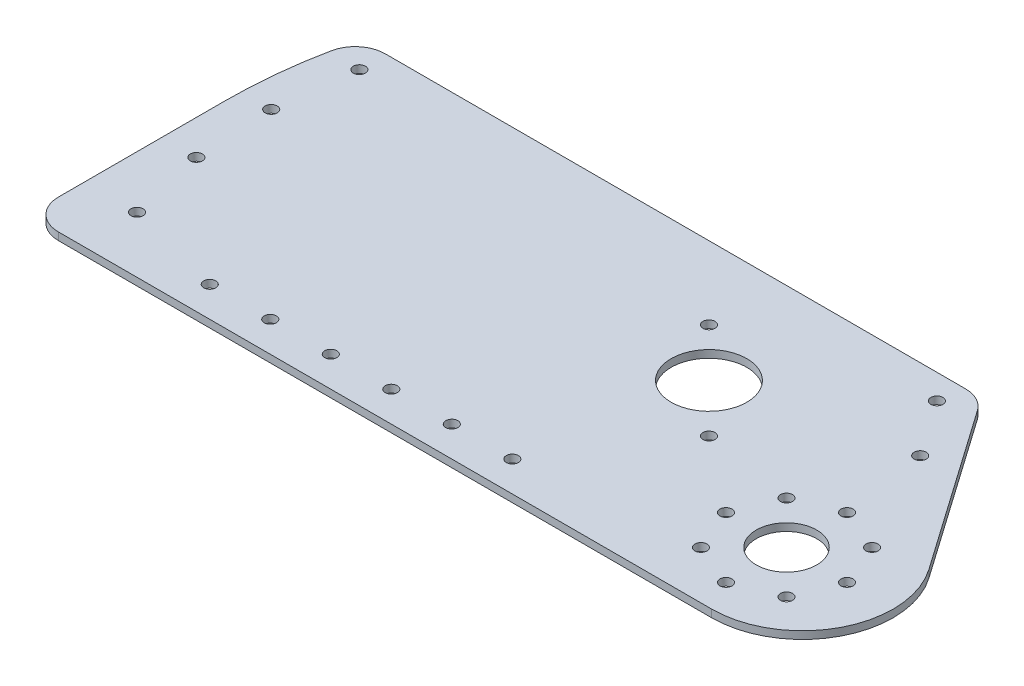
SolidWorks part; units mm, degrees
material "6061 Alloy"
ref_plane "Front Plane" through (0, 0, 0) normal (0, 0, 1) x (1, 0, 0)
ref_plane "Top Plane" through (0, 0, 0) normal (0, 1, 0) x (1, 0, 0)
ref_plane "Right Plane" through (0, 0, 0) normal (1, 0, 0) x (0, 0, -1)
sketch "Sketch1" plane through (0, 0, 0) normal (0, 1, 0) x (1, 0, 0)
  line L0 (0, 0) -> (76.9897, -44.45) construction
  line L1 (0, 0) -> (0, 50.8) construction
  line L2 (-186.6511, 50.8) -> (56.8888, 50.8)
  line L3 (67.292, 45.3844) -> (114.8929, -22.5967)
  line L4 (83.6833, -82.55) -> (-190.5, -82.55)
  line L5 (-203.2, 0) -> (-203.2, -69.85)
  circle A0 centre (0, 0) radius 15.875
  circle A1 centre (76.9897, -44.45) radius 12.7
  arc A3 (67.292, 45.3844) -> (56.8888, 50.8) centre (56.8888, 38.1) ccw
  arc A4 (-199.0945, 40.64) -> (-203.2, 0) centre (0, 0) ccw
  arc A5 (-186.6511, 50.8) -> (-199.0945, 40.64) centre (-186.6511, 38.1) ccw
  circle A6 centre (0, 0) radius 50.8 construction
  arc A7 (-190.5, -82.55) -> (-203.2, -69.85) centre (-190.5, -69.85) cw
  arc A9 (83.6833, -82.55) -> (114.8929, -22.5967) centre (83.6833, -44.45) ccw
  point P9 (97.2008, -16.2467)
  point P14 (63.5, 50.8)
  point P21 (97.2008, -16.2467)
  point P22 (97.2008, -16.2467)
  point P23 (100.6837, -22.3507)
  point P24 (121.1013, -6.8013)
  point P25 (179.646, -65.346)
  point P26 (76.9897, -82.55)
  point P27 (0, 0)
  point P28 (76.9897, -82.55)
  point P29 (152.7563, -82.55)
  point P30 (197.1461, -82.55)
  point P31 (194.4461, -80.1461)
  point P32 (203.3465, -82.55)
  point P33 (196.7823, -82.55)
  point P34 (197.9022, -82.55)
  dimension "D1" = 31.75
  dimension "D3" = 25.4
  dimension "D9" = 125
  dimension "D10" = 12.7
  dimension "D11" = 12.7
  dimension "D12" = 12.7
  dimension "FlyWheel Diameter" = 101.6
  dimension "D7" = 38.1
  dimension "D2" = 88.9
  dimension "D4" = 30
  dimension "D5" = 50.8
  dimension "D6" = 63.5
  dimension "D8" = 38.1
  dimension "BallGapAndBack" = 152.4
extrude "Initial Plate" add sketch "Sketch1" along normal blind 3.175
sketch "Sketch2" plane through (0, 3.175, 0) normal (0, 1, 0) x (1, 0, 0)
  line L0 (47.9962, 50.8) -> (104.4897, -29.8812) construction
  line L1 (114.8929, -22.5967) -> (67.292, 45.3844) construction
  line L2 (56.8888, 50.8) -> (-186.6511, 50.8) construction
  line L3 (104.4897, -29.8812) -> (114.8929, -22.5967) construction
  circle A0 centre (55.2806, 40.3968) radius 2.54
  point P6 (97.4464, -21.9982)
  point P8 (99.69, -20.682)
  point P9 (0, 0)
  point P14 (0, 0)
  point P16 (0, 0)
  dimension "ShooterFrontSupportBoltHole" = 5.08
  dimension "D1" = 12.7
  dimension "D2" = 12.7
extrude "Initial Hole Front" cut sketch "Sketch2" against normal through all
pattern_linear "Front Support Mounts" count 2 spacing 28.575 along (0.5736, 0, 0.8192) of "Initial Hole Front"
sketch "Sketch3" plane through (0, 3.175, 0) normal (0, 1, 0) x (1, 0, 0)
  line L0 (59.0291, -26.4895) -> (94.9502, -62.4105) construction
  line L1 (51.5897, -44.45) -> (102.3897, -44.45) construction
  circle A0 centre (76.9897, -44.45) radius 25.4 construction
  circle A1 centre (59.0291, -26.4895) radius 2.54
  circle A2 centre (102.3897, -44.45) radius 2.54
  circle A3 centre (94.9502, -62.4105) radius 2.54
  circle A4 centre (51.5897, -44.45) radius 2.54
  dimension "D1" = 50.8
  dimension "D2" = 45
  dimension "D3" = 5.08
extrude "Max Planetary Holes" cut sketch "Sketch3" against normal through all
pattern_circular "Max Planetary Pattern" count 3 every 90 about axis through (76.9897, 0, 44.45) along (0, 1, 0) of "Max Planetary Holes"
sketch "Sketch4" plane through (0, 3.175, 0) normal (0, 1, 0) x (1, 0, 0)
  line L0 (-202.171, 20.4234) -> (-176.8996, 17.8705) construction
  line L1 (-50.8, 0) -> (-177.8, 0) construction
  line L2 (-194.6833, 47.9374) -> (-186.3399, 39.594) construction
  line L3 (-203.2, 0) -> (-203.2, -69.85) construction
  line L4 (-203.2, 0) -> (-203.2, -69.85) construction
  circle A0 centre (0, 0) radius 177.8 construction
  arc A1 (-199.0945, 40.64) -> (-203.2, 0) centre (0, 0) ccw construction
  circle A2 centre (0, 0) radius 190.5 construction
  circle A3 centre (-186.3399, 39.594) radius 2.54
  arc A4 (-186.6511, 50.8) -> (-199.0945, 40.64) centre (-186.6511, 38.1) ccw construction
  circle A5 centre (0, 0) radius 50.8 construction
  point P9 (-189.5353, 19.147)
  point P21 (-114.3, 0)
  dimension "D1" = 25.4
  dimension "D2" = 5.08
  dimension "D4" = 101.6
  dimension "D3" = 45
  dimension "Ball Center Dist" = 88.9
extrude "Initial Static Hood Mount" cut sketch "Sketch4" against normal through all
pattern_circular "Hood Mounting Pattern" count 4 every 10 about axis through (0, 0, 0) along (0, 1, 0) of "Initial Static Hood Mount"
sketch "Sketch5" plane through (0, 3.175, 0) normal (0, 1, 0) x (1, 0, 0)
  line L0 (-190.5, -69.85) -> (83.6833, -69.85) construction
  line L1 (-190.5, -82.55) -> (83.6833, -82.55) construction
  line L2 (-190.5, -69.85) -> (-190.5, -82.55) construction
  line L3 (83.6833, -82.55) -> (83.6833, -69.85) construction
  line L4 (-203.2, 0) -> (-203.2, -69.85) construction
  circle A0 centre (-139.7, -69.85) radius 2.54
  point P7 (62.9161, -76.2)
  point P8 (0, 0)
  dimension "D2" = 5.08
  dimension "D1" = 12.7
  dimension "D3" = 63.5
extrude "Initial Mounting Hole" cut sketch "Sketch5" against normal through all
pattern_linear "Mounting Pattern" count 6 spacing 25.4 along (1, 0, 0) of "Initial Mounting Hole"
sketch "Sketch6" plane through (0, 3.175, 0) normal (0, 1, 0) x (1, 0, 0)
  line L0 (-20.2056, 20.2056) -> (20.2056, -20.2056) construction
  line L2 (-190.5, -82.55) -> (83.6833, -82.55) construction
  circle A0 centre (0, 0) radius 28.575 construction
  circle A1 centre (0, 0) radius 15.875 construction
  circle A2 centre (-20.2056, 20.2056) radius 2.54
  circle A3 centre (20.2056, -20.2056) radius 2.54
  dimension "D1" = 12.7
  dimension "D2" = 5.08
  dimension "D3" = 45
extrude "Bearing Retainer Mount" cut sketch "Sketch6" against normal through all
